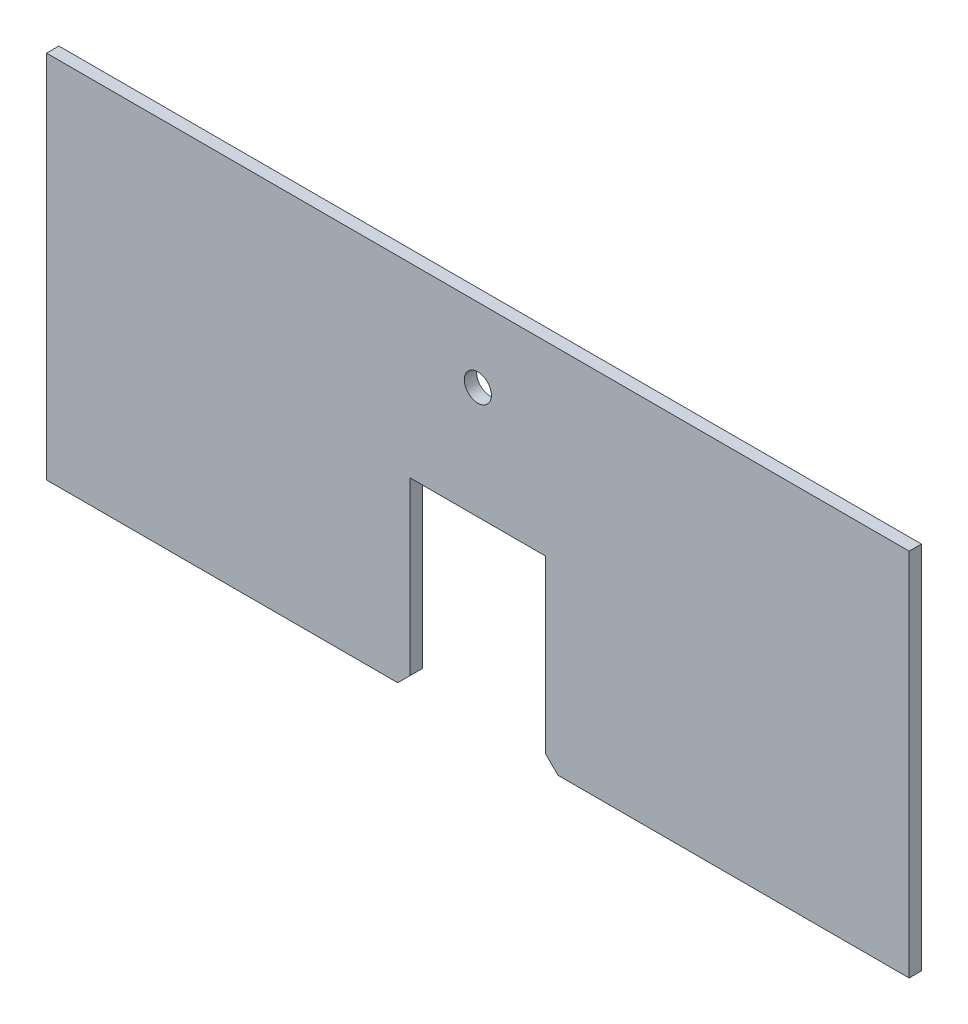
SolidWorks part; units mm, degrees
material "Plain Carbon Steel"
ref_plane "Front Plane" through (0, 0, 0) normal (0, 0, 1) x (1, 0, 0)
ref_plane "Top Plane" through (0, 0, 0) normal (0, 1, 0) x (1, 0, 0)
ref_plane "Right Plane" through (0, 0, 0) normal (1, 0, 0) x (0, 0, -1)
sketch "Sketch1" plane through (0, 0, 0) normal (0, 0, 1) x (1, 0, 0)
  line B0 (350, 232.4214) -> (-350, 232.4214)
  line B1 (-350, 232.4214) -> (-350, -67.5786)
  line B2 (-350, -67.5786) -> (-65, -67.5786)
  line B3 (-65, -67.5786) -> (-55, -57.5786)
  line B4 (-55, 81.4214) -> (55, 81.4214)
  line B5 (-55, -57.5786) -> (-55, 81.4214)
  line B6 (55, -57.5786) -> (55, 81.4214)
  line B7 (65, -67.5786) -> (55, -57.5786)
  line B8 (350, -67.5786) -> (65, -67.5786)
  line B9 (350, 232.4214) -> (350, -67.5786)
sketch_block_instance "Ballast_block-1"
sketch_block "Ballast_block" parameters "D1"=135, "D2"=10, "D3"=230, "D4"=230, "D5"=299, "D6"=285
extrude "Boss-Extrude1" add sketch "Sketch1" along normal mid plane 10
sketch "Sketch2" plane through (0, 0, 0) normal (0, 0, 1) x (1, 0, 0)
  line L0 (0, 0) -> (0, 241.1048) construction
  line L1 (350, 232.4214) -> (-350, 232.4214) construction
  circle A0 centre (0, 172.4214) radius 11
  dimension "D1" = 22
  dimension "D2" = 60
extrude "Cut-Extrude1" cut sketch "Sketch2" against normal through all and the other way through all
